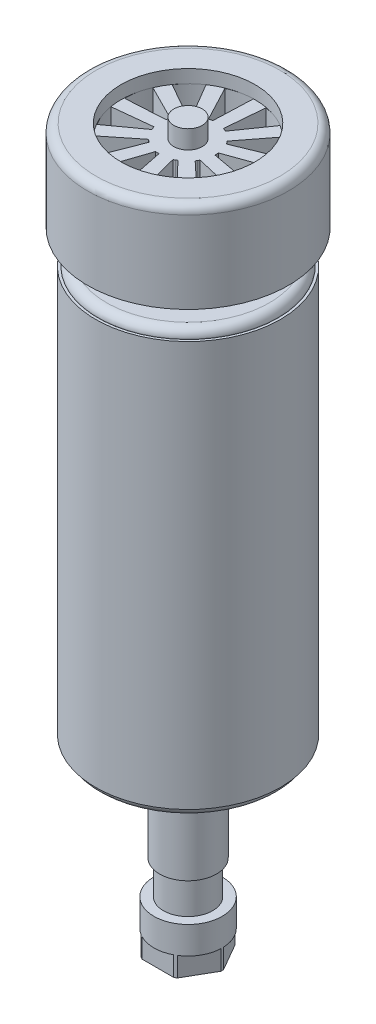
SolidWorks part; units mm, degrees
material "1.0035 (S185)"
ref_plane "Alzado" through (0, 0, 0) normal (0, 0, 1) x (1, 0, 0)
ref_plane "Planta" through (0, 0, 0) normal (0, 1, 0) x (1, 0, 0)
ref_plane "Vista lateral" through (0, 0, 0) normal (1, 0, 0) x (0, 0, -1)
sketch "Croquis3" plane through (0, 0, 0) normal (0, 0, 1) x (1, 0, 0)
  line L0 (0, 66.5033) -> (0, -133.4967) construction
  line L1 (-25.85, 65.0199) -> (-18.85, 65.0199)
  line L2 (-28.25, 62.6199) -> (-28.25, 39.6199)
  line L3 (-28.25, 39.6199) -> (-13, 39.6199)
  line L4 (-13, 39.6199) -> (-13, 32.7199)
  line L5 (-13, 32.7199) -> (-22.9, 32.7199)
  line L6 (-25.3, 30.3199) -> (-25.3, 30.2199)
  line L7 (-25.3, 30.2199) -> (-26, 30.2199)
  line L8 (-26, 30.2199) -> (-26, -83.7801)
  line L9 (-26, -83.7801) -> (-25.3, -83.7801)
  line L10 (-25.3, -83.7801) -> (-25.3, -83.8801)
  line L11 (-22.9, -86.2801) -> (-13, -86.2801)
  line L12 (-13, -92.8801) -> (-4.75, -92.8801)
  line L13 (-9.6, -136.5801) -> (0, -136.5801)
  line L14 (0, -136.5801) -> (0, 66.5033)
  line L15 (-18.85, 65.0199) -> (-18.85, 61.3199)
  line L16 (-18.85, 61.3199) -> (-4, 61.3199)
  line L17 (-4, 61.3199) -> (-4, 66.5033)
  line L18 (0, -133.4967) -> (0, 66.5033) construction
  line L19 (-13, -86.2801) -> (-13, -92.8801)
  line L20 (-4.75, -92.8801) -> (-4.75, -93.8801)
  line L21 (-4.75, -93.8801) -> (-8, -93.8801)
  line L22 (-8, -93.8801) -> (-8, -113.8801)
  line L23 (-8, -113.8801) -> (-6.9, -113.8801)
  line L24 (-6.9, -113.8801) -> (-6.9, -123.3801)
  line L25 (-6.9, -123.3801) -> (-9.6, -123.3801)
  line L26 (-9.6, -123.3801) -> (-9.6, -136.5801)
  line L27 (-4, 66.5033) -> (0, 66.5033)
  arc A0 (-25.3, 30.3199) -> (-22.9, 32.7199) centre (-22.9, 30.3199) cw
  arc A1 (-22.9, -86.2801) -> (-25.3, -83.8801) centre (-22.9, -83.8801) cw
  arc A2 (-28.25, 62.6199) -> (-25.85, 65.0199) centre (-25.85, 62.6199) cw
  point P26 (-6.375, -93.8801)
  dimension "D9" = 2.4
  dimension "D13" = 2.4
  dimension "D24" = 2.4
  dimension "D1" = 200
  dimension "D2" = 28.25
  dimension "D3" = 25.4
  dimension "D4" = 13
  dimension "D5" = 6.9
  dimension "D6" = 2.5
  dimension "D7" = 26
  dimension "D8" = 25.3
  dimension "D10" = 114
  dimension "D11" = 25.3
  dimension "D12" = 2.5
  dimension "D14" = 13
  dimension "D15" = 6.6
  dimension "D16" = 4.75
  dimension "D17" = 8
  dimension "D18" = 1
  dimension "D19" = 20
  dimension "D20" = 9.5
  dimension "D21" = 6.9
  dimension "D22" = 9.6
  dimension "D23" = 13.2
  dimension "D25" = 9.4
  dimension "D26" = 3.7
  dimension "D27" = 4
revolve "Revolución1" add sketch "Croquis3" angle 360 about L0
sketch "Croquis4" plane through (0, 61.3199, 0) normal (0, 1, 0) x (1, 0, 0)
  line L0 (-7.6582, 1.4794) -> (-18.6901, 0.8471)
  line L1 (-18.3732, 4.213) -> (-6.1604, 1.6795) construction
  line L2 (-5.6426, 5.3848) -> (-15.2652, 10.8173)
  line L3 (-7.455, 2.4589) -> (-17.3251, 7.4273)
  line L4 (-4.9421, 6.099) -> (-10.5593, 15.6149)
  line L5 (-1.8356, 7.5807) -> (-6.9936, 17.353)
  line L6 (-0.8602, 7.8027) -> (-0.441, 18.8448)
  line L7 (2.5542, 7.3697) -> (3.4983, 18.3793)
  line L8 (3.4948, 7.0291) -> (9.8173, 16.0917)
  line L9 (6.1331, 4.8189) -> (12.8796, 13.5703)
  line L10 (6.7403, 4.0239) -> (16.9587, 8.2296)
  line L11 (7.7647, 0.7381) -> (18.1717, 4.4528)
  line L12 (7.8457, -0.259) -> (18.7158, -2.2454)
  line L13 (6.9312, -3.577) -> (17.6944, -6.0784)
  line L14 (6.4602, -4.4596) -> (14.5308, -12.0075)
  line L15 (3.897, -6.7564) -> (11.5992, -14.6798)
  line L16 (3.0237, -7.2443) -> (5.7323, -17.9572)
  line L17 (-0.3745, -7.7907) -> (1.8214, -18.6204)
  line L18 (-1.3729, -7.729) -> (-4.8861, -18.2057)
  line L19 (-4.527, -6.3515) -> (-8.5347, -16.6492)
  line L20 (-5.3336, -5.7598) -> (-13.9532, -12.674)
  line L21 (-7.2423, -2.8958) -> (-16.1811, -9.392)
  line L22 (-7.6009, -1.9619) -> (-18.5903, -3.1184)
  circle A0 centre (0, 0) radius 7.85 construction
  circle A1 centre (0, 0) radius 18.85 construction
  circle A2 centre (0, 0) radius 18.85 construction
  arc A3 (-7.455, 2.4589) -> (-7.5968, 1.9775) centre (0, 0) ccw
  arc A4 (-17.3251, 7.4273) -> (-18.6901, 0.8471) centre (-3.2006, 1.0655) ccw
  arc A5 (-7.6582, 1.4794) -> (-7.5968, 1.9775) centre (0.1597, 0.7699) cw
  arc A6 (-10.5593, 15.6149) -> (-15.2652, 10.8173) centre (-2.1164, 2.6267) ccw
  arc A7 (-4.9421, 6.099) -> (-5.3218, 5.7707) centre (0, 0) ccw
  arc A8 (-5.6426, 5.3848) -> (-5.3218, 5.7707) centre (0.5506, 0.5614) cw
  arc A9 (-0.441, 18.8448) -> (-6.9936, 17.353) centre (-0.3604, 3.354) ccw
  arc A10 (-0.8602, 7.8027) -> (-1.3571, 7.7318) centre (0, 0) ccw
  arc A11 (-1.8356, 7.5807) -> (-1.3571, 7.7318) centre (0.7667, 0.1746) cw
  arc A12 (9.8173, 16.0917) -> (3.4983, 18.3793) centre (1.5101, 3.0164) ccw
  arc A13 (3.4948, 7.0291) -> (3.0385, 7.2381) centre (0, 0) ccw
  arc A14 (2.5542, 7.3697) -> (3.0385, 7.2381) centre (0.7394, -0.2677) cw
  arc A15 (16.9587, 8.2296) -> (12.8796, 13.5703) centre (2.9012, 1.7211) ccw
  arc A16 (6.7403, 4.0239) -> (6.4694, 4.4463) centre (0, 0) ccw
  arc A17 (6.1331, 4.8189) -> (6.4694, 4.4463) centre (0.4773, -0.6249) cw
  arc A18 (18.7158, -2.2454) -> (18.1717, 4.4528) centre (3.3711, -0.1206) ccw
  arc A19 (7.8457, -0.259) -> (7.8462, 0.2429) centre (0, 0) ccw
  arc A20 (7.7647, 0.7381) -> (7.8462, 0.2429) centre (0.0637, -0.7837) cw
  arc A21 (14.5308, -12.0075) -> (17.6944, -6.0784) centre (2.7707, -1.924) ccw
  arc A22 (6.4602, -4.4596) -> (6.732, -4.0377) centre (0, 0) ccw
  arc A23 (6.9312, -3.577) -> (6.732, -4.0377) centre (-0.3702, -0.6937) cw
  arc A24 (5.7323, -17.9572) -> (11.5992, -14.6798) centre (1.2907, -3.1166) ccw
  arc A25 (3.0237, -7.2443) -> (3.4804, -7.0363) centre (0, 0) ccw
  arc A26 (3.897, -6.7564) -> (3.4804, -7.0363) centre (-0.6865, -0.3835) cw
  arc A27 (-4.8861, -18.2057) -> (1.8214, -18.6204) centre (-0.5992, -3.3196) ccw
  arc A28 (-1.3729, -7.729) -> (-0.8762, -7.8009) centre (0, 0) ccw
  arc A29 (-0.3745, -7.7907) -> (-0.8762, -7.8009) centre (-0.7848, 0.0485) cw
  arc A30 (-13.9532, -12.674) -> (-8.5347, -16.6492) centre (-2.2988, -2.4687) ccw
  arc A31 (-5.3336, -5.7598) -> (-4.9546, -6.0889) centre (0, 0) ccw
  arc A32 (-4.527, -6.3515) -> (-4.9546, -6.0889) centre (-0.634, 0.4651) cw
  arc A33 (-18.5903, -3.1184) -> (-16.1811, -9.392) centre (-3.2685, -0.834) ccw
  arc A34 (-7.6009, -1.9619) -> (-7.46, -2.4436) centre (0, 0) ccw
  arc A35 (-7.2423, -2.8958) -> (-7.46, -2.4436) centre (-0.2819, 0.7341) cw
  point P89 (0, 0)
  dimension "D1" = 11
  dimension "D2" = 15
  dimension "D3" = 11
extrude "Cortar-Extruir1" cut sketch "Croquis4" against normal blind 22
sketch "Croquis5" plane through (0, -136.5801, 0) normal (0, -1, 0) x (1, 0, 0)
  line L1 (9.815, 0) -> (4.9075, 8.5)
  line L2 (4.9075, 8.5) -> (-4.9075, 8.5)
  line L3 (-4.9075, 8.5) -> (-9.815, 0)
  line L4 (-9.815, 0) -> (-4.9075, -8.5)
  line L5 (-4.9075, -8.5) -> (4.9075, -8.5)
  line L6 (4.9075, -8.5) -> (9.815, 0)
  circle A0 centre (0, 0) radius 8.5 construction
  circle A1 centre (-0.0969, 0) radius 1.5
  dimension "D2" = 3
  dimension "D1" = 17
extrude "Cortar-Extruir2" cut sketch "Croquis5" against normal blind 5.5 flip side to cut
sketch "Croquis6" plane through (0, -86.2801, 0) normal (0, -1, 0) x (1, 0, 0)
  circle A0 centre (0, 17.5) radius 1.5
  circle A2 centre (17.5, 0) radius 1.5
  circle A3 centre (0, -17.5) radius 1.5
  circle A4 centre (-17.5, 0) radius 1.5
  point P12 (0, 0)
  dimension "D2" = 3
  dimension "D1" = 17.5
  dimension "D3" = 4
extrude "Cortar-Extruir3" cut sketch "Croquis6" against normal blind 10
